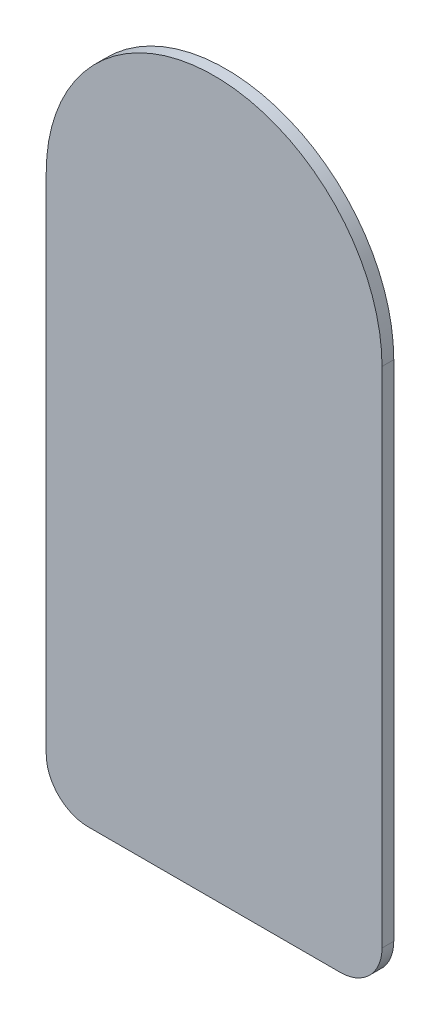
SolidWorks part; units mm, degrees
ref_plane "Front Plane" through (0, 0, 0) normal (0, 0, 1) x (1, 0, 0)
ref_plane "Top Plane" through (0, 0, 0) normal (0, 1, 0) x (1, 0, 0)
ref_plane "Right Plane" through (0, 0, 0) normal (1, 0, 0) x (0, 0, -1)
sketch "Sketch1" plane through (0, 0, 0) normal (0, 0, 1) x (1, 0, 0)
  point P0 (0, 0)
  line B0 (10.16, -30.48) -> (10.16, 0)
  line B1 (-10.16, 0) -> (-10.16, -30.48)
  line B2 (-7.62, -33.02) -> (7.62, -33.02)
  arc B3 (7.62, -33.02) -> (10.16, -30.48) centre (7.62, -30.48) ccw
  arc B4 (10.16, 0) -> (-10.16, 0) centre (0, 0) ccw
  arc B5 (-10.16, -30.48) -> (-7.62, -33.02) centre (-7.62, -30.48) ccw
sketch_block_instance "Block1-1"
sketch_block "Block1"
extrude "Boss-Extrude1" add sketch "Sketch1" along normal blind 0.7112
